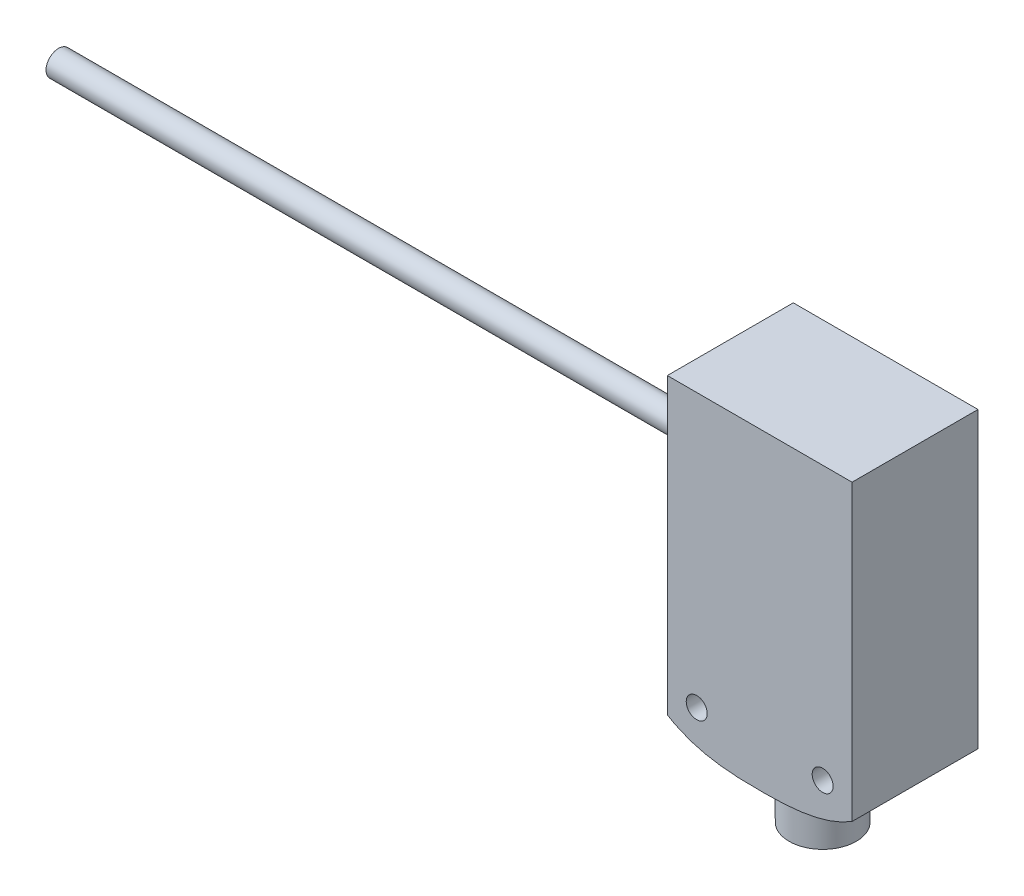
SolidWorks part; units mm, degrees
ref_plane "Plan de face" through (0, 0, 0) normal (0, 0, 1) x (1, 0, 0)
ref_plane "Plan de dessus" through (0, 0, 0) normal (0, 1, 0) x (1, 0, 0)
ref_plane "Plan de droite" through (0, 0, 0) normal (1, 0, 0) x (0, 0, -1)
sketch "Esquisse1" plane through (0, 0, 0) normal (0, 0, 1) x (1, 0, 0)
  line L0 (0, 0) -> (0, 44.3) construction
  line L1 (-11, 0) -> (11, 0)
  line L2 (11, 0) -> (11, 44.3)
  line L3 (11, 44.3) -> (-11, 44.3)
  line L4 (-11, 0) -> (-11, 44.3)
  circle A0 centre (7.5, 11.8) radius 1.25
  circle A1 centre (-7.5, 11.8) radius 1.25
  dimension "D3" = 2.5
  dimension "D4" = 11.8
  dimension "D5" = 15
  dimension "D1" = 22
  dimension "D2" = 44.3
extrude "Boss.-Extru.1" add sketch "Esquisse1" along normal blind 15
sketch "Esquisse2" plane through (0, 0, 15) normal (0, 0, 1) x (1, 0, 0)
  line L0 (0, 0) -> (0, 44.3) construction
  line L1 (-11, 0) -> (11, 0) construction
  line L2 (11, 44.3) -> (-11, 44.3) construction
  line L3 (11, 0) -> (11, 44.3) construction
  line L4 (-11, 9.3) -> (-11, 0)
  line L5 (-11, 0) -> (11, 0)
  line L6 (11, 0) -> (11, 9.3)
  spline S0 degree 3 poles (-11, 9.3) (-7.6254, 7.2367) (0, 6.7633) (7.6254, 7.2367) (11, 9.3) knots 0 0 0 0 0.5 1 1 1 1
  point P6 (0, 7)
  point P7 (11, 9.3)
  point P8 (5.8, 7.4)
  point P11 (-5.8, 7.4)
  point P12 (-11, 9.3)
  dimension "D1" = 37.3
  dimension "D2" = 35
  dimension "D3" = 36.9
  dimension "D4" = 5.8
extrude "Enlèv. mat.-Extru.1" cut sketch "Esquisse2" against normal through all
sketch "Esquisse3" plane through (0, 0, 0) normal (0, 1, 0) x (1, 0, 0)
  line L0 (11, 0) -> (-11, -15) construction
  circle A0 centre (0, -7.5) radius 4
  dimension "D1" = 8
extrude "Boss.-Extru.2" add sketch "Esquisse3" along normal up to next
sketch "Esquisse4" plane through (-11, 0, 0) normal (-1, 0, 0) x (0, 0, 1)
  line L0 (7.5, 44.3) -> (7.5, 9.3) construction
  line L1 (15, 44.3) -> (0, 44.3) construction
  line L2 (0, 9.3) -> (15, 9.3) construction
  line L3 (1.3, 37.8) -> (13.7, 37.8)
  line L4 (13.7, 37.8) -> (13.7, 16.8)
  line L5 (15, 44.3) -> (15, 9.3) construction
  line L6 (1.3, 37.8) -> (1.3, 16.8)
  arc A0 (1.3, 16.8) -> (13.7, 16.8) centre (7.5, 35.8147) ccw
  point P13 (7.5, 37.8)
  dimension "D3" = 20
  dimension "D1" = 6.5
  dimension "D2" = 1.3
  dimension "D4" = 21
extrude "Enlèv. mat.-Extru.2" cut sketch "Esquisse4" against normal blind 0.1
sketch "Esquisse5" plane through (-11, 0, 0) normal (-1, 0, 0) x (0, 0, 1)
  line L0 (7.5, 37.8) -> (7.5, 9.3) construction
  line L1 (13.7, 37.8) -> (1.3, 37.8) construction
  line L2 (0, 9.3) -> (15, 9.3) construction
  circle A0 centre (7.5, 32.8) radius 1.5
  dimension "D1" = 3
  dimension "D2" = 5
extrude "Boss.-Extru.3" add sketch "Esquisse5" along normal blind 80 separate body
